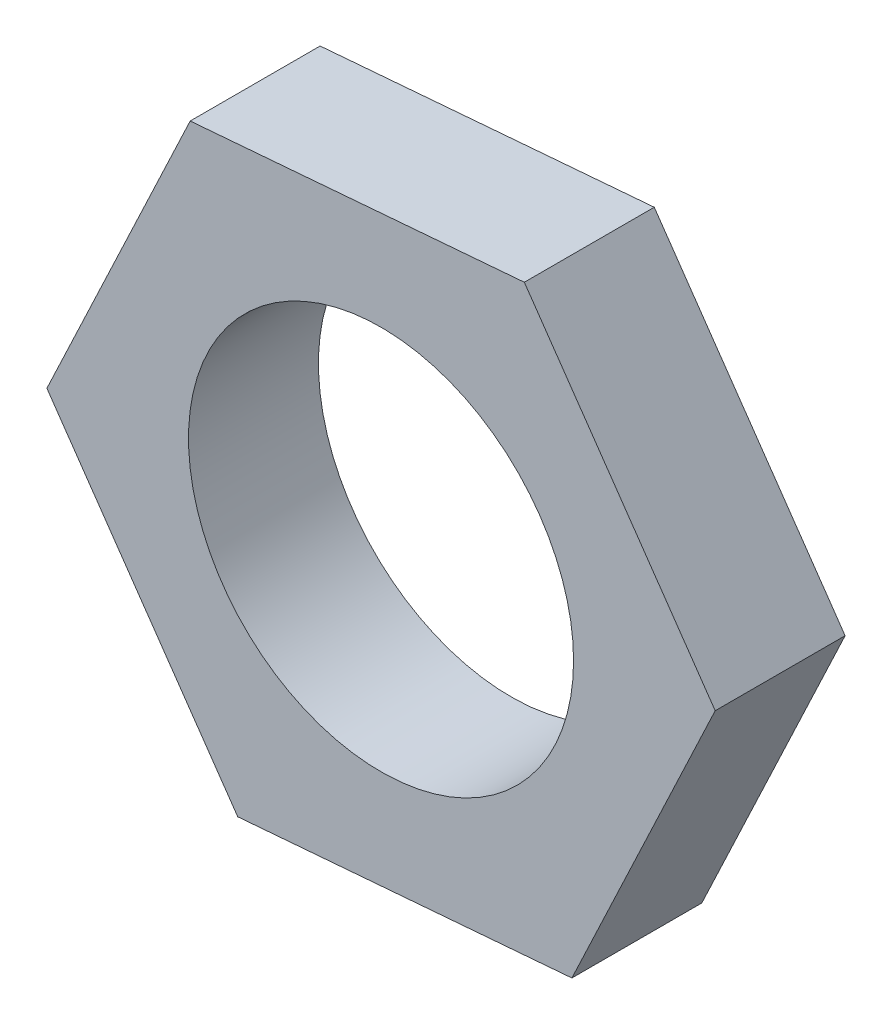
SolidWorks part; units mm, degrees
material "Stop odlewniczy stali"
ref_plane "Płaszczyzna przednia" through (0, 0, 0) normal (0, 0, 1) x (1, 0, 0)
ref_plane "Płaszczyzna górna" through (0, 0, 0) normal (0, 1, 0) x (1, 0, 0)
ref_plane "Płaszczyzna prawa" through (0, 0, 0) normal (1, 0, 0) x (0, 0, -1)
sketch "Szkic1" plane through (0, 0, 0) normal (0, 0, 1) x (1, 0, 0)
  line L1 (-4.5539, 6.5774) -> (-7.9731, -0.6551)
  line L2 (-7.9731, -0.6551) -> (-3.4192, -7.2325)
  line L3 (-3.4192, -7.2325) -> (4.5539, -6.5774)
  line L4 (4.5539, -6.5774) -> (7.9731, 0.6551)
  line L5 (7.9731, 0.6551) -> (3.4192, 7.2325)
  line L6 (3.4192, 7.2325) -> (-4.5539, 6.5774)
  circle A1 centre (0, 0) radius 6.9282 construction
extrude "Dodanie-wyciągnięcie1" add sketch "Szkic1" along normal blind 3.1
sketch "Szkic4" plane through (0, 0, 3.1) normal (0, 0, 1) x (1, 0, 0)
  circle A0 centre (0, 0) radius 4.594
extrude "Wytnij-wyciągnięcie1" cut sketch "Szkic4" against normal blind 3.1
